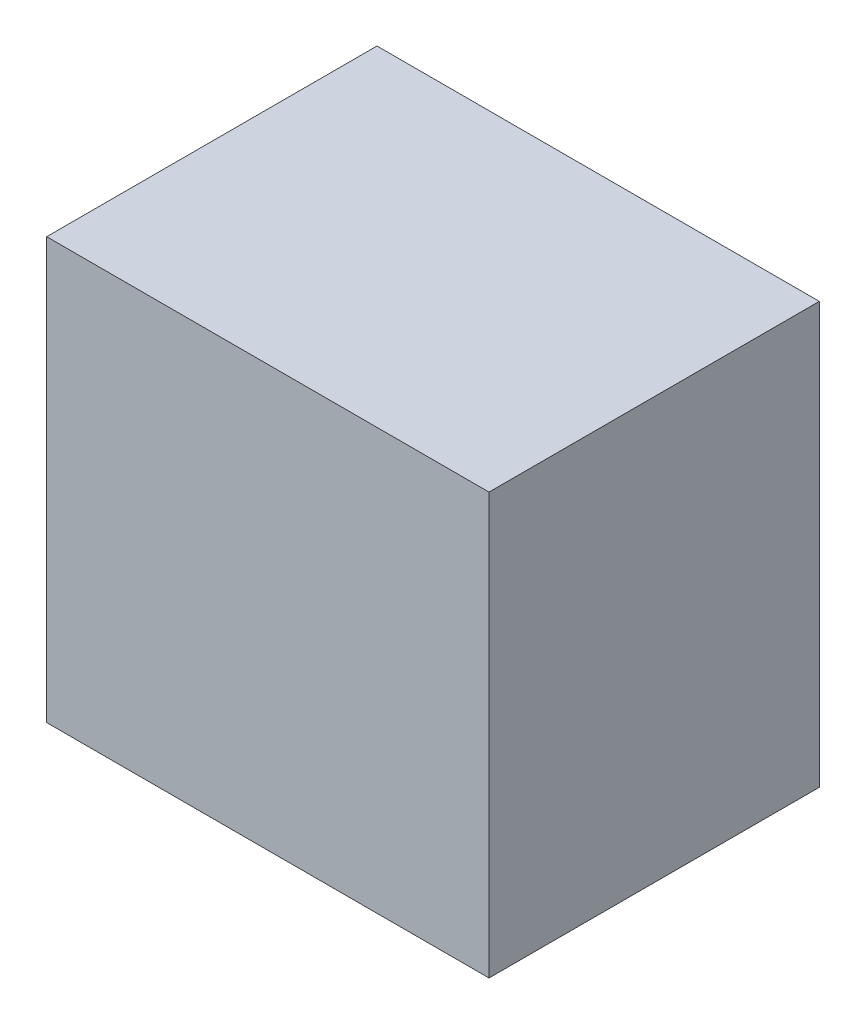
SolidWorks part; units mm, degrees
ref_plane "Front Plane" through (0, 0, 0) normal (0, 0, 1) x (1, 0, 0)
ref_plane "Top Plane" through (0, 0, 0) normal (0, 1, 0) x (1, 0, 0)
ref_plane "Right Plane" through (0, 0, 0) normal (1, 0, 0) x (0, 0, -1)
sketch "Sketch1" plane through (0, 0, 0) normal (0, 1, 0) x (1, 0, 0)
  line L1 (-117.7219, -87.9047) -> (117.7219, -87.9047)
  line L2 (-117.7219, -87.9047) -> (-117.7219, 87.9047)
  line L3 (-117.7219, 87.9047) -> (117.7219, 87.9047)
  line L4 (117.7219, -87.9047) -> (117.7219, 87.9047)
  line L5 (-117.7219, -87.9047) -> (117.7219, 87.9047) construction
  line L6 (-117.7219, 87.9047) -> (117.7219, -87.9047) construction
  point P0 (0, 0)
extrude "Boss-Extrude1" add sketch "Sketch1" along normal mid plane 224
